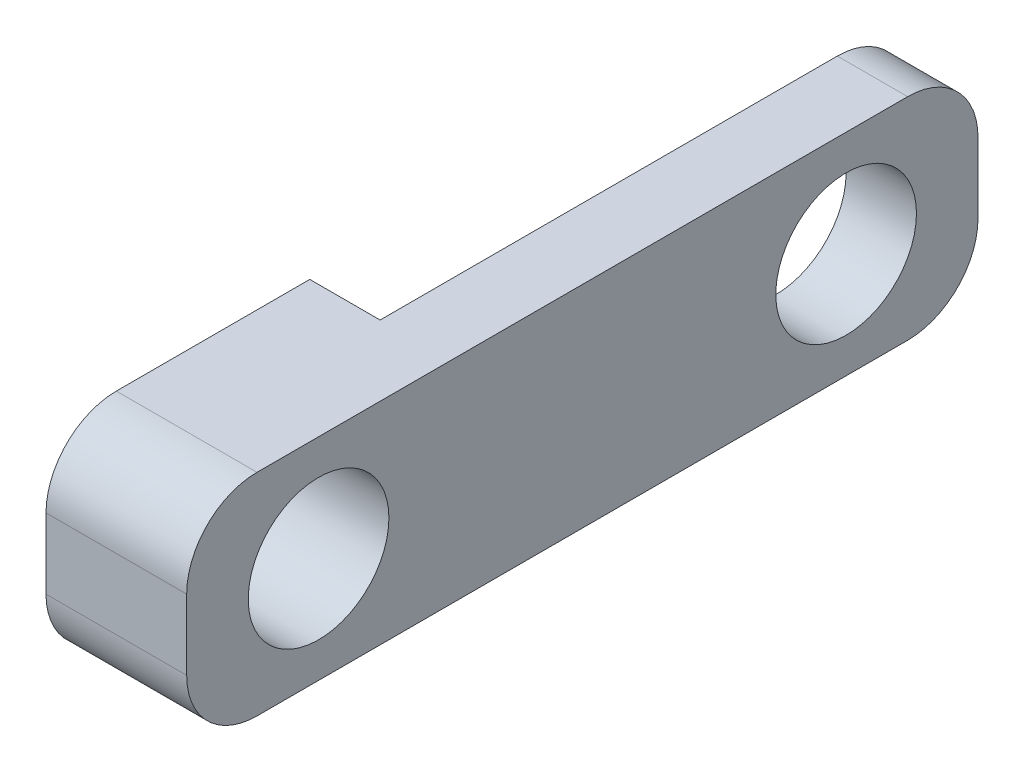
SolidWorks part; units mm, degrees
ref_plane "Front Plane" through (0, 0, 0) normal (0, 0, 1) x (1, 0, 0)
ref_plane "Top Plane" through (0, 0, 0) normal (0, 1, 0) x (1, 0, 0)
ref_plane "Right Plane" through (0, 0, 0) normal (1, 0, 0) x (0, 0, -1)
sketch "Sketch1" plane through (0, 0, 0) normal (1, 0, 0) x (0, 0, -1)
  line L1 (-22.5, 6) -> (22.5, 6)
  line L2 (-22.5, 6) -> (-22.5, -6)
  line L3 (-22.5, -6) -> (22.5, -6)
  line L4 (22.5, 6) -> (22.5, -6)
  line L5 (-22.5, 6) -> (22.5, -6) construction
  line L6 (-22.5, -6) -> (22.5, 6) construction
  point P0 (0, 0)
  dimension "D1" = 12
  dimension "D2" = 45
extrude "Boss-Extrude1" add sketch "Sketch1" along normal blind 8
sketch "Sketch2" plane through (8, 0, 0) normal (1, 0, 0) x (0, 0, -1)
  line L0 (-22.5, 6) -> (-22.5, -6) construction
  line L1 (22.5, -6) -> (22.5, 6) construction
  circle A0 centre (-15, 0) radius 4
  circle A1 centre (15, 0) radius 4
  dimension "D3" = 8
  dimension "D4" = 8
  dimension "D1" = 7.5
  dimension "D5" = 7.5
extrude "Cut-Extrude1" cut sketch "Sketch2" against normal blind 8
fillet "Fillet1" radius 4 4 edges at (4, -6, -22.5) (4, -6, 22.5) (4, 6, -22.5) (4, 6, 22.5)
sketch "Sketch3" plane through (0, 6, 0) normal (0, 1, 0) x (1, 0, 0)
  line L0 (8, -22.5) -> (0, -22.5) construction
  line L1 (4, -7.5) -> (0, -7.5)
  line L2 (4, -7.5) -> (4, 32.3306)
  line L3 (4, 32.3306) -> (0, 32.3306)
  line L4 (0, -7.5) -> (0, 32.3306)
  dimension "D1" = 4
  dimension "D2" = 15
extrude "Cut-Extrude2" cut sketch "Sketch3" against normal blind 16
